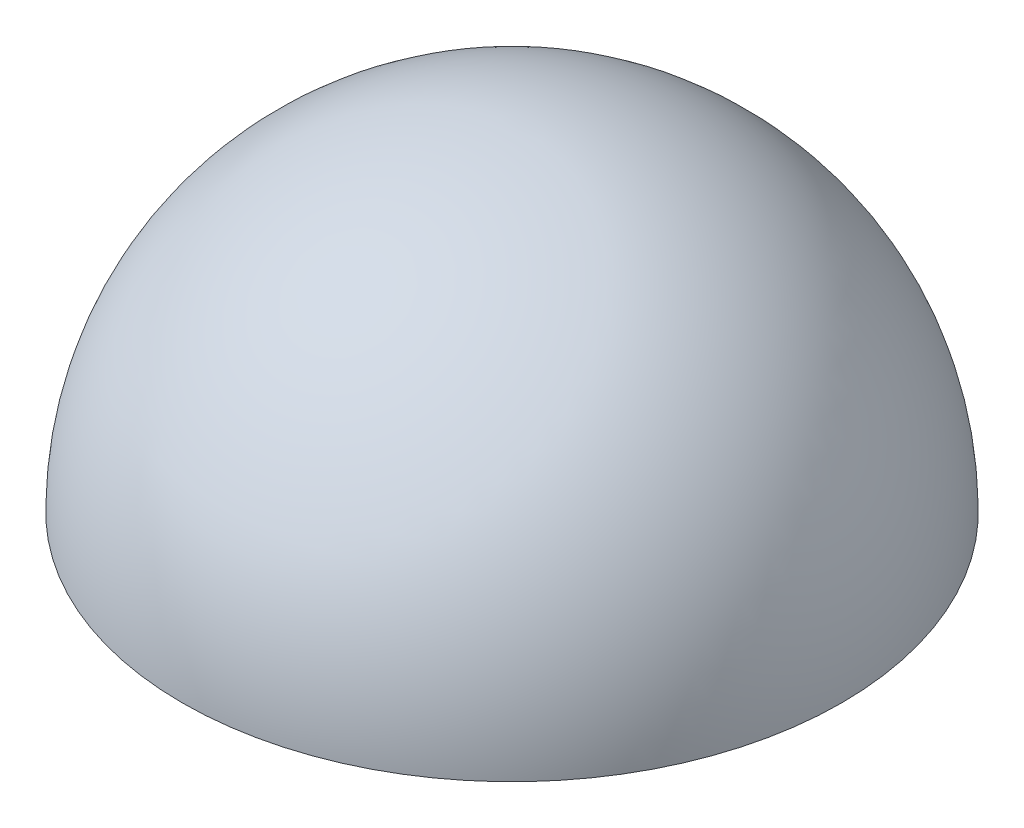
SolidWorks part; units mm, degrees
ref_plane "Front Plane" through (0, 0, 0) normal (0, 0, 1) x (1, 0, 0)
ref_plane "Top Plane" through (0, 0, 0) normal (0, 1, 0) x (1, 0, 0)
ref_plane "Right Plane" through (0, 0, 0) normal (1, 0, 0) x (0, 0, -1)
sketch "Sketch8" plane through (0, 0, 0) normal (0, 0, 1) x (1, 0, 0)
  line L0 (0, -5) -> (0, 0) construction
  line L2 (0, 5) -> (0, -5)
  arc A1 (0, -5) -> (0, 5) centre (0, 0) ccw
  dimension "D1" = 5
revolve "Revolve5" add sketch "Sketch8" angle 360 about L0
sketch "Sketch9" plane through (0, 0, 0) normal (0, 1, 0) x (1, 0, 0)
  circle A0 centre (0, 0) radius 5
  dimension "D1" = 10
extrude "Cut-Extrude1" cut sketch "Sketch9" against normal blind 5
sketch "Sketch10" plane through (0, 0, 0) normal (0, -1, 0) x (1, 0, 0)
  point P0 (0, 0)
